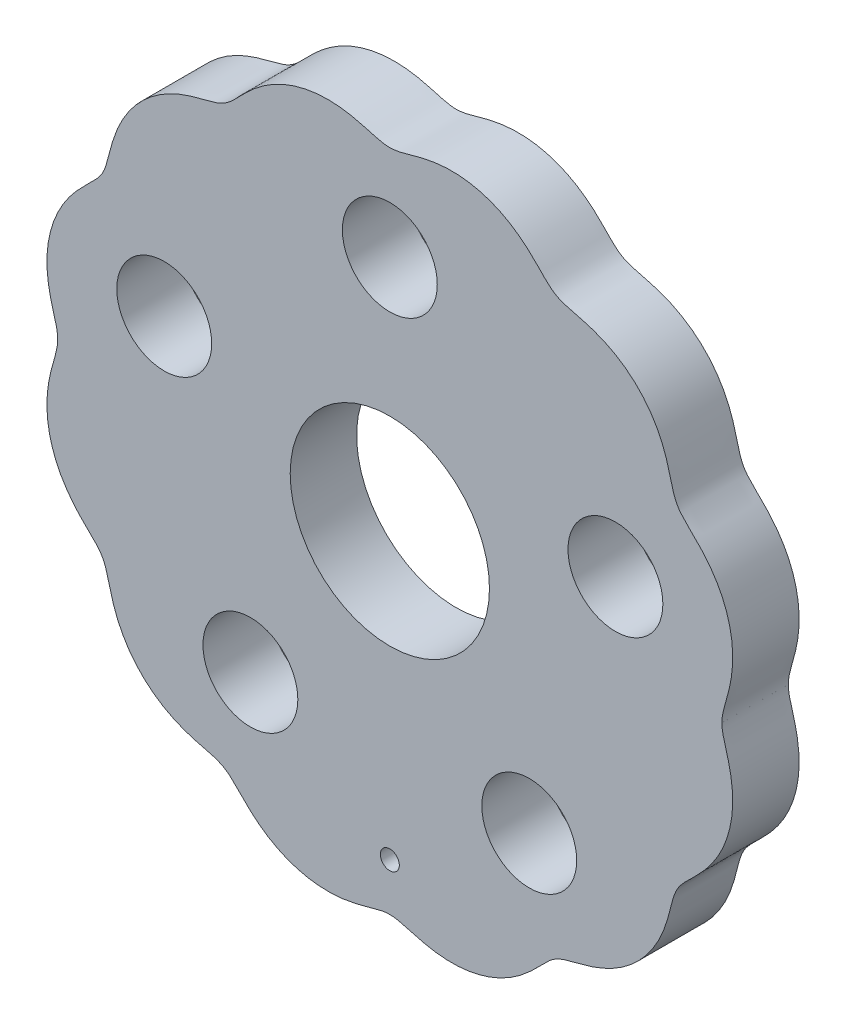
SolidWorks part; units mm, degrees
ref_plane "Front Plane" through (0, 0, 0) normal (0, 0, 1) x (1, 0, 0)
ref_plane "Top Plane" through (0, 0, 0) normal (0, 1, 0) x (1, 0, 0)
ref_plane "Right Plane" through (0, 0, 0) normal (1, 0, 0) x (0, 0, -1)
sketch "Sketch1" plane through (0, 0, 0) normal (0, 0, 1) x (1, 0, 0)
  spline S0 degree 4 poles (29.8719, 18.5427) (29.9086, 18.4234) (29.9873, 18.187) (30.123, 17.8375) (30.3574, 17.3962) (30.7505, 16.8405) (31.3465, 16.2199) (32.1039, 15.5109) (32.9564, 14.639) (33.8056, 13.6193) (34.6026, 12.4247) (35.2588, 11.1101) (35.7463, 9.6908) (36.0289, 8.3453) (36.1507, 7.1018) (36.1452, 5.9021) (36.0321, 4.7575) (35.8546, 3.813) (35.6696, 3.0639) (35.515, 2.5019) (35.407, 2.1227) (35.2991, 1.7434) (35.2091, 1.4103) (35.1394, 1.1227) (35.0892, 0.8817) (35.0549, 0.6867) (35.0311, 0.5166) (35.0159, 0.3719) (35.007, 0.2432) (35.0022, 0.1362) (34.9994, 0.0216) (35.0001, -0.0775) (35.0065, -0.2547) (35.0203, -0.4218) (35.0404, -0.5863) (35.0662, -0.7532) (35.1045, -0.9602) (35.1587, -1.2064) (35.2307, -1.4921) (35.3199, -1.8164) (35.412, -2.14) (35.5222, -2.5274) (35.6466, -2.9799) (35.8141, -3.6452) (35.9932, -4.5308) (36.1261, -5.5773) (36.1616, -6.7876) (36.0739, -8.0002) (35.8479, -9.2723) (35.4582, -10.5841) (34.9129, -11.8403) (34.2223, -13.0213) (33.4521, -14.0647) (32.638, -14.9786) (31.8008, -15.797) (30.9923, -16.5612) (30.3358, -17.3532) (29.9547, -18.2066) (29.7211, -19.0571) (29.5204, -19.8766) (29.2912, -20.7474) (28.9995, -21.6628) (28.623, -22.6098) (28.1404, -23.5742) (27.5548, -24.5229) (26.859, -25.4412) (25.9578, -26.4108) (24.8147, -27.3771) (23.5698, -28.1695) (22.2557, -28.7851) (21.036, -29.2112) (19.9414, -29.5091) (19.0073, -29.7287) (18.1454, -29.9808) (17.4895, -30.2919) (16.892, -30.7043) (16.2427, -31.3246) (15.5855, -32.0237) (14.7802, -32.8228) (13.8014, -33.6661) (12.6113, -34.4964) (11.3027, -35.1784) (9.8943, -35.6853) (8.6039, -35.9811) (7.4608, -36.1246) (6.3464, -36.1574) (5.2699, -36.0932) (4.2615, -35.9458) (3.3229, -35.7408) (2.4542, -35.5039) (1.6442, -35.268) (0.7908, -35.0449) (-0.1388, -34.9481) (-1.1529, -35.1205) (-2.219, -35.4386) (-3.3464, -35.7545) (-4.5449, -36.0026) (-5.8336, -36.148) (-7.2017, -36.1556) (-8.5622, -35.9999) (-9.8932, -35.6816) (-11.1079, -35.2413) (-12.2019, -34.711) (-13.2323, -34.0752) (-14.1922, -33.3457) (-14.9858, -32.6245) (-15.644, -31.9556) (-16.202, -31.3745) (-16.6813, -30.9021) (-17.2017, -30.4725) (-17.7877, -30.134) (-18.4199, -29.898) (-19.0686, -29.719) (-19.8509, -29.5263) (-20.7593, -29.2907) (-21.7807, -28.9642) (-22.8924, -28.4978) (-23.9584, -27.9234) (-24.9647, -27.2413) (-25.9534, -26.4096) (-26.8947, -25.4163) (-27.71, -24.316) (-28.3876, -23.1274) (-28.9061, -21.9387) (-29.2906, -20.7768) (-29.5808, -19.6425) (-29.8384, -18.5602) (-30.1958, -17.5957) (-30.7441, -16.8388) (-31.364, -16.2112) (-31.9732, -15.6277) (-32.6128, -14.9938) (-33.2598, -14.2835) (-33.8917, -13.484) (-34.4857, -12.5839) (-35.0145, -11.6024) (-35.4619, -10.5408) (-35.8512, -9.2755) (-36.1166, -7.8024) (-36.1804, -6.3281) (-36.0566, -4.8823) (-35.8158, -3.6129) (-35.5265, -2.5159) (-35.2497, -1.5971) (-35.037, -0.7248) (-34.9782, -0.0012) (-35.0366, 0.7225) (-35.249, 1.5949) (-35.5259, 2.5137) (-35.8153, 3.6106) (-36.0563, 4.88) (-36.1804, 6.3258) (-36.1168, 7.8001) (-35.8517, 9.2732) (-35.4627, 10.5386) (-35.0155, 11.6003) (-34.4869, 12.5819) (-33.893, 13.4821) (-33.2613, 14.2818) (-32.6144, 14.9921) (-31.9749, 15.6261) (-31.3656, 16.2096) (-30.7457, 16.8371) (-30.1969, 17.5936) (-29.839, 18.558) (-29.5814, 19.6403) (-29.2913, 20.7746) (-28.907, 21.9366) (-28.3887, 23.1254) (-27.7113, 24.314) (-26.8962, 25.4145) (-25.9551, 26.408) (-24.9665, 27.2399) (-23.9603, 27.9222) (-22.8945, 28.4968) (-21.7828, 28.9634) (-20.7615, 29.2901) (-19.8531, 29.5258) (-19.0708, 29.7184) (-18.4221, 29.8973) (-17.7898, 30.1331) (-17.2036, 30.4712) (-16.683, 30.9006) (-16.2037, 31.3728) (-15.7498, 31.8454) (-15.3041, 32.301) (-14.8593, 32.7327) (-14.4127, 33.1364) (-13.8341, 33.6178) (-13.106, 34.153) (-12.2039, 34.7099) (-11.11, 35.2404) (-9.8954, 35.6809) (-8.5645, 35.9995) (-7.204, 36.1555) (-5.8359, 36.1482) (-4.5472, 36.0029) (-3.3487, 35.755) (-2.2212, 35.4392) (-1.1552, 35.1211) (-0.1411, 34.9482) (0.7885, 35.0444) (1.642, 35.2674) (2.4519, 35.5033) (3.3207, 35.7402) (4.2592, 35.9454) (5.2676, 36.093) (6.3441, 36.1574) (7.4585, 36.1247) (8.6016, 35.9815) (9.8921, 35.686) (11.3005, 35.1794) (12.6093, 34.4976) (13.7995, 33.6675) (14.7785, 32.8243) (15.5839, 32.0254) (16.2411, 31.3263) (16.8902, 30.7058) (17.4874, 30.293) (18.1433, 29.9816) (19.005, 29.7293) (19.9391, 29.5097) (21.0338, 29.2118) (22.2536, 28.786) (23.5678, 28.1706) (24.8128, 27.3785) (25.9561, 26.4124) (26.8575, 25.4429) (27.5535, 24.5248) (28.1393, 23.5762) (28.6221, 22.6119) (28.9987, 21.665) (29.2906, 20.7496) (29.5198, 19.8788) (29.7205, 19.0594) (29.9539, 18.2088) (30.3345, 17.3552) (30.9906, 16.5629) (31.7991, 15.7986) (32.6364, 14.9802) (33.4506, 14.0665) (34.2211, 13.0233) (34.9118, 11.8423) (35.4574, 10.5863) (35.8474, 9.2745) (36.0736, 8.0025) (36.1615, 6.7899) (36.1263, 5.5796) (35.9935, 4.5331) (35.8146, 3.6475) (35.6471, 2.9821) (35.5229, 2.5296) (35.4126, 2.1423) (35.3205, 1.8185) (35.2313, 1.4945) (35.149, 1.1676) (35.0873, 0.8807) (35.0458, 0.6298) (35.0205, 0.4244) (35.0066, 0.2558) (34.9991, 0.0531) (34.9995, -0.0713) (35.0087, -0.3034) (35.0275, -0.4877) (35.0545, -0.6852) (35.0887, -0.8792) (35.1389, -1.1205) (35.2085, -1.408) (35.2985, -1.7412) (35.4064, -2.1204) (35.5144, -2.4996) (35.6309, -2.9232) (35.7508, -3.3925) (35.8989, -4.049) (36.0459, -4.8983) (36.145, -5.8997) (36.1508, -7.0994) (36.0292, -8.3429) (35.747, -9.6885) (35.2597, -11.1078) (34.6039, -12.4225) (33.8071, -13.6173) (32.9581, -14.6371) (32.1058, -15.5091) (31.3484, -16.2182) (30.7522, -16.8386) (30.3588, -17.394) (30.1241, -17.8352) (29.9882, -18.1846) (29.9094, -18.4209) (29.8727, -18.5402) knots 0 0 0 0 0 0.001814 0.003629 0.005443 0.007258 0.01169 0.016123 0.020556 0.024988 0.030982 0.036976 0.041873 0.04677 0.050949 0.055128 0.059307 0.063486 0.064921 0.066356 0.067791 0.069226 0.070661 0.071378 0.072096 0.072813 0.07353 0.073889 0.074248 0.074607 0.074965 0.075577 0.07619 0.076802 0.077414 0.078026 0.078638 0.079862 0.081086 0.082311 0.083535 0.084759 0.086949 0.08914 0.09352 0.097901 0.102281 0.106733 0.111185 0.116671 0.122156 0.126608 0.131059 0.13551 0.139961 0.143623 0.147285 0.150351 0.153416 0.156482 0.159548 0.163466 0.167384 0.171303 0.175221 0.179673 0.184125 0.190536 0.196947 0.201072 0.205197 0.209323 0.213448 0.215046 0.218242 0.21984 0.223965 0.22809 0.232215 0.23634 0.242751 0.249162 0.253614 0.258066 0.261985 0.265903 0.269822 0.27374 0.276805 0.279871 0.282937 0.286002 0.289664 0.293326 0.297777 0.302228 0.30668 0.311131 0.316617 0.322102 0.326554 0.331006 0.335387 0.339767 0.344148 0.348528 0.350977 0.353425 0.355874 0.358322 0.360771 0.363219 0.365667 0.368116 0.372496 0.376877 0.381258 0.385638 0.39009 0.394542 0.400028 0.405513 0.409965 0.414416 0.418867 0.423318 0.42698 0.430642 0.433708 0.436773 0.439839 0.442904 0.446823 0.450741 0.454659 0.458578 0.46303 0.467482 0.473893 0.480304 0.484429 0.488554 0.492679 0.496805 0.498403 0.501599 0.503197 0.507322 0.511447 0.515572 0.519697 0.526108 0.532519 0.536971 0.541423 0.545342 0.54926 0.553178 0.557097 0.560162 0.563228 0.566293 0.569359 0.573021 0.576683 0.581134 0.585585 0.590037 0.594488 0.599974 0.605459 0.609911 0.614363 0.618743 0.623124 0.627505 0.631885 0.634334 0.636782 0.639231 0.641679 0.644127 0.646576 0.649024 0.651473 0.653663 0.655853 0.658044 0.660234 0.664614 0.668995 0.673447 0.677899 0.683384 0.68887 0.693321 0.697773 0.702224 0.706675 0.710337 0.713999 0.717065 0.72013 0.723196 0.726261 0.73018 0.734098 0.738016 0.741935 0.746387 0.750839 0.75725 0.763661 0.767786 0.771911 0.776036 0.780161 0.781759 0.784955 0.786553 0.790679 0.794804 0.798929 0.803054 0.809465 0.815876 0.820328 0.82478 0.828698 0.832617 0.836535 0.840453 0.843519 0.846585 0.84965 0.852716 0.856378 0.86004 0.864491 0.868942 0.873393 0.877845 0.88333 0.888816 0.893268 0.89772 0.9021 0.906481 0.910861 0.913052 0.915242 0.916466 0.917691 0.918915 0.920139 0.921363 0.922587 0.923199 0.923812 0.924424 0.925036 0.925753 0.926471 0.927188 0.927905 0.928623 0.92934 0.930775 0.93221 0.933645 0.93508 0.936514 0.938604 0.940694 0.944873 0.949052 0.953231 0.958128 0.963025 0.969019 0.975012 0.979445 0.983877 0.98831 0.992742 0.994557 0.996371 0.998186 1 1 1 1 1 construction
  spline S1 degree 4 poles (35, 0) (35, -0.0357) (35.0012, -0.1064) (35.0065, -0.2547) (35.0203, -0.4218) (35.0404, -0.5863) (35.0662, -0.7532) (35.1045, -0.9602) (35.1587, -1.2064) (35.2307, -1.4921) (35.3199, -1.8164) (35.412, -2.14) (35.5222, -2.5274) (35.6466, -2.9799) (35.8141, -3.6452) (35.9932, -4.5308) (36.1261, -5.5773) (36.1616, -6.7876) (36.0739, -8.0002) (35.8479, -9.2723) (35.4582, -10.5841) (34.9129, -11.8403) (34.2223, -13.0213) (33.4521, -14.0647) (32.638, -14.9786) (31.8008, -15.797) (30.9923, -16.5612) (30.3358, -17.3532) (29.9547, -18.2066) (29.7211, -19.0571) (29.5204, -19.8766) (29.2912, -20.7474) (28.9995, -21.6628) (28.623, -22.6098) (28.1404, -23.5742) (27.5548, -24.5229) (26.859, -25.4412) (25.9578, -26.4108) (24.8147, -27.3771) (23.5698, -28.1695) (22.2557, -28.7851) (21.036, -29.2112) (19.9414, -29.5091) (19.0073, -29.7287) (18.1454, -29.9808) (17.4895, -30.2919) (16.892, -30.7043) (16.2427, -31.3246) (15.5855, -32.0237) (14.7802, -32.8228) (13.8014, -33.6661) (12.6113, -34.4964) (11.3027, -35.1784) (9.8943, -35.6853) (8.6039, -35.9811) (7.4608, -36.1246) (6.3464, -36.1574) (5.2699, -36.0932) (4.2615, -35.9458) (3.3229, -35.7408) (2.4542, -35.5039) (1.6442, -35.268) (0.7908, -35.0449) (-0.1388, -34.9481) (-1.1529, -35.1205) (-2.219, -35.4386) (-3.3464, -35.7545) (-4.5449, -36.0026) (-5.8336, -36.148) (-7.2017, -36.1556) (-8.5622, -35.9999) (-9.8932, -35.6816) (-11.1079, -35.2413) (-12.2019, -34.711) (-13.2323, -34.0752) (-14.1922, -33.3457) (-14.9858, -32.6245) (-15.644, -31.9556) (-16.202, -31.3745) (-16.6813, -30.9021) (-17.2017, -30.4725) (-17.7877, -30.134) (-18.4199, -29.898) (-19.0686, -29.719) (-19.8509, -29.5263) (-20.7593, -29.2907) (-21.7807, -28.9642) (-22.8924, -28.4978) (-23.9584, -27.9234) (-24.9647, -27.2413) (-25.9534, -26.4096) (-26.8947, -25.4163) (-27.71, -24.316) (-28.3876, -23.1274) (-28.9061, -21.9387) (-29.2906, -20.7768) (-29.5808, -19.6425) (-29.8384, -18.5602) (-30.1958, -17.5957) (-30.7441, -16.8388) (-31.364, -16.2112) (-31.9732, -15.6277) (-32.6128, -14.9938) (-33.2598, -14.2835) (-33.8917, -13.484) (-34.4857, -12.5839) (-35.0145, -11.6024) (-35.4619, -10.5408) (-35.8512, -9.2755) (-36.1166, -7.8024) (-36.1804, -6.3281) (-36.0566, -4.8823) (-35.8158, -3.6129) (-35.5265, -2.5159) (-35.2497, -1.5971) (-35.037, -0.7248) (-34.9782, -0.0012) (-35.0366, 0.7225) (-35.249, 1.5949) (-35.5259, 2.5137) (-35.8153, 3.6106) (-36.0563, 4.88) (-36.1804, 6.3258) (-36.1168, 7.8001) (-35.8517, 9.2732) (-35.4627, 10.5386) (-35.0155, 11.6003) (-34.4869, 12.5819) (-33.893, 13.4821) (-33.2613, 14.2818) (-32.6144, 14.9921) (-31.9749, 15.6261) (-31.3656, 16.2096) (-30.7457, 16.8371) (-30.1969, 17.5936) (-29.839, 18.558) (-29.5814, 19.6403) (-29.2913, 20.7746) (-28.907, 21.9366) (-28.3887, 23.1254) (-27.7113, 24.314) (-26.8962, 25.4145) (-25.9551, 26.408) (-24.9665, 27.2399) (-23.9603, 27.9222) (-22.8945, 28.4968) (-21.7828, 28.9634) (-20.7615, 29.2901) (-19.8531, 29.5258) (-19.0708, 29.7184) (-18.4221, 29.8973) (-17.7898, 30.1331) (-17.2036, 30.4712) (-16.683, 30.9006) (-16.2037, 31.3728) (-15.7498, 31.8454) (-15.3041, 32.301) (-14.8593, 32.7327) (-14.4127, 33.1364) (-13.8341, 33.6178) (-13.106, 34.153) (-12.2039, 34.7099) (-11.11, 35.2404) (-9.8954, 35.6809) (-8.5645, 35.9995) (-7.204, 36.1555) (-5.8359, 36.1482) (-4.5472, 36.0029) (-3.3487, 35.755) (-2.2212, 35.4392) (-1.1552, 35.1211) (-0.1411, 34.9482) (0.7885, 35.0444) (1.642, 35.2674) (2.4519, 35.5033) (3.3207, 35.7402) (4.2592, 35.9454) (5.2676, 36.093) (6.3441, 36.1574) (7.4585, 36.1247) (8.6016, 35.9815) (9.8921, 35.686) (11.3005, 35.1794) (12.6093, 34.4976) (13.7995, 33.6675) (14.7785, 32.8243) (15.5839, 32.0254) (16.2411, 31.3263) (16.8902, 30.7058) (17.4874, 30.293) (18.1433, 29.9816) (19.005, 29.7293) (19.9391, 29.5097) (21.0338, 29.2118) (22.2536, 28.786) (23.5678, 28.1706) (24.8128, 27.3785) (25.9561, 26.4124) (26.8575, 25.4429) (27.5535, 24.5248) (28.1393, 23.5762) (28.6221, 22.6119) (28.9987, 21.665) (29.2906, 20.7496) (29.5198, 19.8788) (29.7205, 19.0594) (29.9539, 18.2088) (30.3345, 17.3552) (30.9906, 16.5629) (31.7991, 15.7986) (32.6364, 14.9802) (33.4506, 14.0665) (34.2211, 13.0233) (34.9118, 11.8423) (35.4574, 10.5863) (35.8474, 9.2745) (36.0736, 8.0025) (36.1615, 6.7899) (36.1263, 5.5796) (35.9935, 4.5331) (35.8146, 3.6475) (35.6471, 2.9821) (35.5229, 2.5296) (35.4126, 2.1423) (35.3205, 1.8185) (35.2313, 1.4945) (35.149, 1.1676) (35.0873, 0.8807) (35.0458, 0.6298) (35.0205, 0.4244) (35.0066, 0.2558) (35.0012, 0.1101) (35, 0.0381) (35, 0.0023) knots 0.074965 0.074965 0.074965 0.074965 0.074965 0.075577 0.07619 0.076802 0.077414 0.078026 0.078638 0.079862 0.081086 0.082311 0.083535 0.084759 0.086949 0.08914 0.09352 0.097901 0.102281 0.106733 0.111185 0.116671 0.122156 0.126608 0.131059 0.13551 0.139961 0.143623 0.147285 0.150351 0.153416 0.156482 0.159548 0.163466 0.167384 0.171303 0.175221 0.179673 0.184125 0.190536 0.196947 0.201072 0.205197 0.209323 0.213448 0.215046 0.218242 0.21984 0.223965 0.22809 0.232215 0.23634 0.242751 0.249162 0.253614 0.258066 0.261985 0.265903 0.269822 0.27374 0.276805 0.279871 0.282937 0.286002 0.289664 0.293326 0.297777 0.302228 0.30668 0.311131 0.316617 0.322102 0.326554 0.331006 0.335387 0.339767 0.344148 0.348528 0.350977 0.353425 0.355874 0.358322 0.360771 0.363219 0.365667 0.368116 0.372496 0.376877 0.381258 0.385638 0.39009 0.394542 0.400028 0.405513 0.409965 0.414416 0.418867 0.423318 0.42698 0.430642 0.433708 0.436773 0.439839 0.442904 0.446823 0.450741 0.454659 0.458578 0.46303 0.467482 0.473893 0.480304 0.484429 0.488554 0.492679 0.496805 0.498403 0.501599 0.503197 0.507322 0.511447 0.515572 0.519697 0.526108 0.532519 0.536971 0.541423 0.545342 0.54926 0.553178 0.557097 0.560162 0.563228 0.566293 0.569359 0.573021 0.576683 0.581134 0.585585 0.590037 0.594488 0.599974 0.605459 0.609911 0.614363 0.618743 0.623124 0.627505 0.631885 0.634334 0.636782 0.639231 0.641679 0.644127 0.646576 0.649024 0.651473 0.653663 0.655853 0.658044 0.660234 0.664614 0.668995 0.673447 0.677899 0.683384 0.68887 0.693321 0.697773 0.702224 0.706675 0.710337 0.713999 0.717065 0.72013 0.723196 0.726261 0.73018 0.734098 0.738016 0.741935 0.746387 0.750839 0.75725 0.763661 0.767786 0.771911 0.776036 0.780161 0.781759 0.784955 0.786553 0.790679 0.794804 0.798929 0.803054 0.809465 0.815876 0.820328 0.82478 0.828698 0.832617 0.836535 0.840453 0.843519 0.846585 0.84965 0.852716 0.856378 0.86004 0.864491 0.868942 0.873393 0.877845 0.88333 0.888816 0.893268 0.89772 0.9021 0.906481 0.910861 0.913052 0.915242 0.916466 0.917691 0.918915 0.920139 0.921363 0.922587 0.923199 0.923812 0.924424 0.925036 0.925036 0.925036 0.925036 0.925036
  spline S2 degree 1 poles (35, 0.0023) (35, 0) knots 0 0 1 1
extrude "Boss-Extrude2" add sketch "Sketch1" along normal blind 7 contours S1 S2
sketch "Sketch3" plane through (0, 0, 7) normal (0, 0, 1) x (1, 0, 0)
  circle A0 centre (0, 0) radius 10.5
  circle A2 centre (0, 25.0003) radius 5
  circle A4 centre (23.7767, 7.7255) radius 5
  circle A6 centre (14.6948, -20.2257) radius 5
  circle A8 centre (-14.6948, -20.2257) radius 5
  circle A9 centre (0, 0) radius 25.0003 construction
  circle A10 centre (-23.7767, 7.7255) radius 5
  point P24 (0, 0)
  dimension "D1" = 21
  dimension "D2" = 10
  dimension "D4" = 50.0006
  dimension "D3" = 5
extrude "Cut-Extrude1" cut sketch "Sketch3" against normal through all both and the other way through all
sketch "Sketch4" plane through (0, 0, 7) normal (0, 0, 1) x (1, 0, 0)
  circle A0 centre (0, -30) radius 1
  circle A5 centre (14.6948, -20.2257) radius 5 construction
  dimension "D1" = 2
  dimension "D3" = 17.6487
  dimension "D2" = 30
extrude "Cut-Extrude3" cut sketch "Sketch4" against normal through all both and the other way through all
equation "\"R\"= 25"
equation "\"Rr\"= 4"
equation "\"N\"= 13"
equation "\"E\"= 1"
